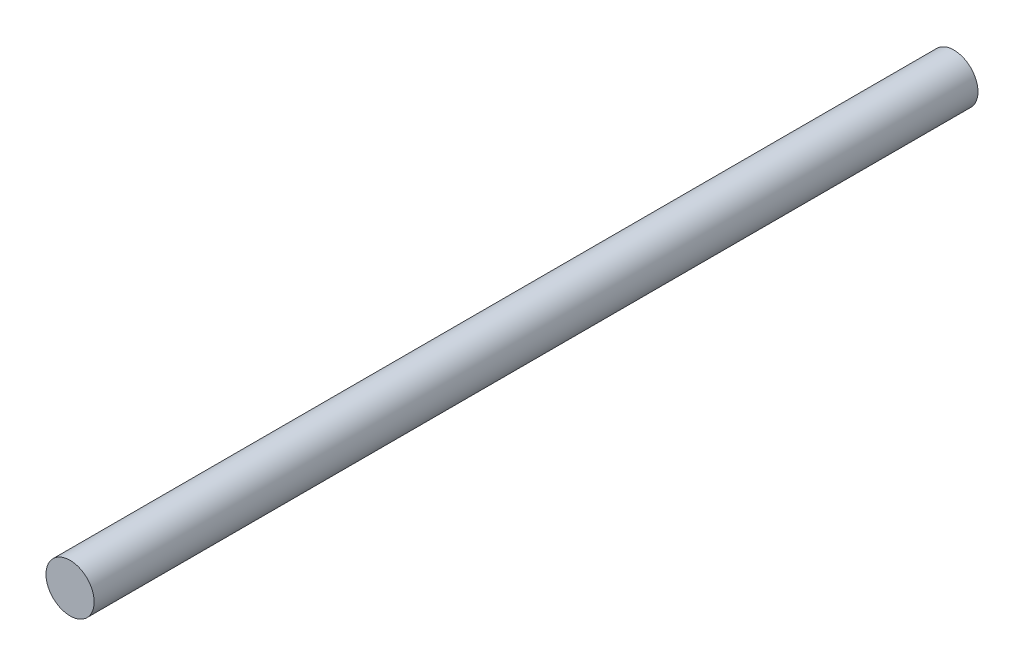
SolidWorks part; units mm, degrees
ref_plane "Front Plane" through (0, 0, 0) normal (0, 0, 1) x (1, 0, 0)
ref_plane "Top Plane" through (0, 0, 0) normal (0, 1, 0) x (1, 0, 0)
ref_plane "Right Plane" through (0, 0, 0) normal (1, 0, 0) x (0, 0, -1)
sketch "Sketch1" plane through (0, 0, 0) normal (0, 0, 1) x (1, 0, 0)
  circle A0 centre (0, 0) radius 1.5
  dimension "D1" = 3
extrude "Boss-Extrude1" add sketch "Sketch1" along normal blind 55
